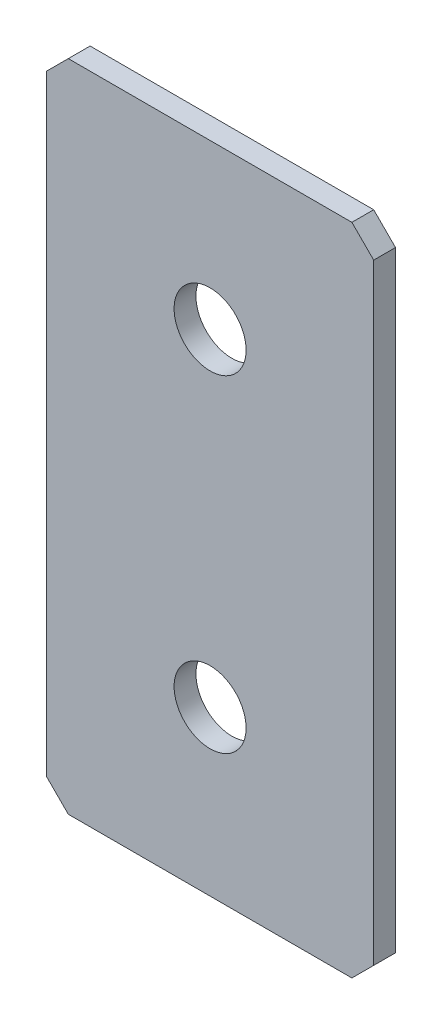
SolidWorks part; units mm, degrees
material "Простая углеродистая сталь"
ref_plane "Спереди(Плоскость XY)" through (0, 0, 0) normal (0, 0, 1) x (1, 0, 0)
ref_plane "Сверху(Плоскость XZ)" through (0, 0, 0) normal (0, 1, 0) x (1, 0, 0)
ref_plane "Справа(Плоскость ZY)" through (0, 0, 0) normal (1, 0, 0) x (0, 0, -1)
sketch "Эскиз1" plane through (0, 0, 0) normal (0, 0, 1) x (1, 0, 0)
  line L1 (-15, -30) -> (15, -30)
  line L2 (-15, -30) -> (-15, 30)
  line L3 (-15, 30) -> (15, 30)
  line L4 (15, -30) -> (15, 30)
  line L5 (-15, -30) -> (15, 30) construction
  line L6 (-15, 30) -> (15, -30) construction
  point P0 (0, 0)
  dimension "D1" = 30
  dimension "D2" = 60
extrude "Бобышка-Вытянуть1" add sketch "Эскиз1" along normal blind 2
chamfer "Фаска1" distance 2 angle 45 4 edges at (-15, -30, 1) (15, -30, 1) (-15, 30, 1) (15, 30, 1)
hole_wizard "Отверстие с зазором M61" positions "Эскиз2" profile "Эскиз3" hole size "M6" standard "DIN" end condition through all
sketch "Эскиз2" plane through (0, 0, 2) normal (0, 0, 1) x (1, 0, 0)
  line L12 (0, 30) -> (0, -30) construction
  line L13 (13, 30) -> (-13, 30) construction
  line L14 (-13, -30) -> (13, -30) construction
  point P204 (0, 45)
  point P206 (0, 15)
  point P208 (0, -15)
  point P210 (0, -45)
  dimension "D1" = 30
  dimension "D2" = 30
  dimension "D3" = 30
  dimension "D4" = 15
sketch "Эскиз3" plane through (0, -45, 2) normal (1, 0, 0) x (0, -1, 0)
  line L0 (0, 0) -> (0, 2)
  line L1 (0, 2) -> (3.3, 2)
  line L2 (3.3, 2) -> (3.3, 0)
  line L5 (3.3, 0) -> (0, 0)
  line L11 (0, -6.35) -> (0, 107.95) construction
  dimension "Диаметр сквозного отверстия" = 6.6
  dimension "Глубина сквозного отверстия" = 2
